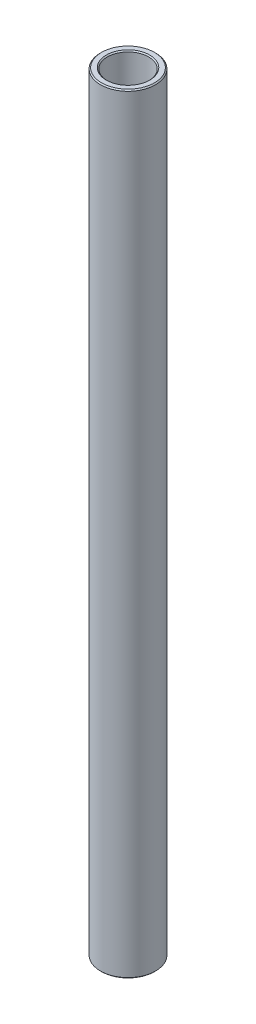
SolidWorks part; units mm, degrees
ref_plane "Front Plane" through (0, 0, 0) normal (0, 0, 1) x (1, 0, 0)
ref_plane "Top Plane" through (0, 0, 0) normal (0, 1, 0) x (1, 0, 0)
ref_plane "Right Plane" through (0, 0, 0) normal (1, 0, 0) x (0, 0, -1)
sketch "Sketch1" plane through (0, 0, 0) normal (0, 0, 1) x (1, 0, 0)
  line L0 (4.7625, 131.7624) -> (4.7625, 309.2226)
  line L1 (4.7625, 309.2226) -> (6.35, 309.2226)
  line L2 (6.35, 309.2226) -> (6.35, 131.7624)
  line L3 (6.35, 131.7624) -> (4.7625, 131.7624)
  line L4 (120.0875, 140.4936) -> (10.0875, 140.4936) construction
  line L6 (0, 122.2374) -> (0, 318.7476) construction
  dimension "D1" = 9.525
  dimension "D2" = 9.525
  dimension "D3" = 12.7
  dimension "D4" = 9.525
revolve "Revolve1" add sketch "Sketch1" angle 360 about L6
chamfer "Chamfer1" distance 0.254 angle 45 4 edges at (6.35, 309.2226, 0) (4.7625, 309.2226, 0) (4.7625, 131.7624, 0) (6.35, 131.7624, 0)
equation "\"D4@Sketch1\"=\"D1@Sketch1\""
